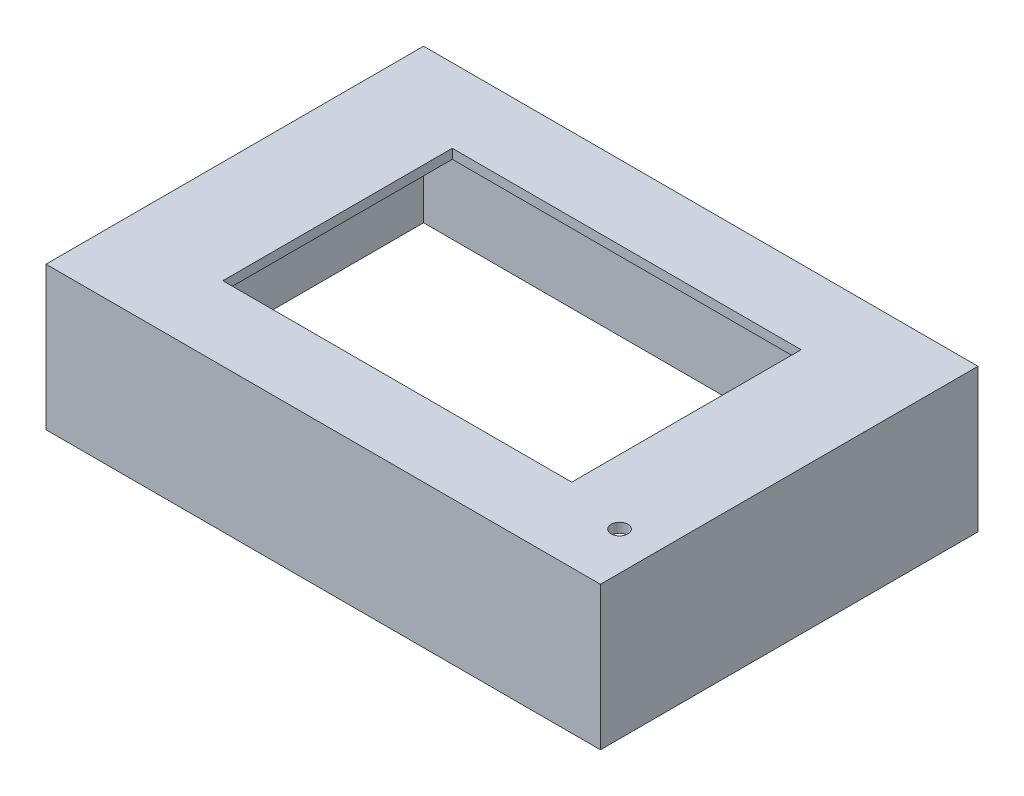
SolidWorks part; units mm, degrees
ref_plane "Front Plane" through (0, 0, 0) normal (0, 0, 1) x (1, 0, 0)
ref_plane "Top Plane" through (0, 0, 0) normal (0, 1, 0) x (1, 0, 0)
ref_plane "Right Plane" through (0, 0, 0) normal (1, 0, 0) x (0, 0, -1)
sketch "Sketch1" plane through (0, 0, 0) normal (0, 1, 0) x (1, 0, 0)
  line L0 (58, 39.5) -> (-58, 39.5)
  line L1 (56, -37.5) -> (-56, -37.5)
  line L2 (56, -37.5) -> (56, 37.5)
  line L3 (56, 37.5) -> (-56, 37.5)
  line L4 (-56, -37.5) -> (-56, 37.5)
  line L5 (56, -37.5) -> (-56, 37.5) construction
  line L6 (56, 37.5) -> (-56, -37.5) construction
  line L7 (-58, -39.5) -> (-58, 39.5)
  line L8 (58, -39.5) -> (-58, -39.5)
  line L9 (58, -39.5) -> (58, 39.5)
  point P0 (0, 0)
  dimension "D1" = 112
  dimension "D2" = 75
  dimension "D3" = 2
extrude "Boss-Extrude1" add sketch "Sketch1" along normal blind 28
sketch "Sketch2" plane through (0, 28, 0) normal (0, 1, 0) x (1, 0, 0)
  line L1 (58, -39.5) -> (-58, -39.5)
  line L2 (58, -39.5) -> (58, 39.5)
  line L3 (58, 39.5) -> (-58, 39.5)
  line L4 (-58, -39.5) -> (-58, 39.5)
  line L5 (58, -39.5) -> (-58, 39.5) construction
  line L6 (58, 39.5) -> (-58, -39.5) construction
  point P0 (0, 0)
extrude "Boss-Extrude2" add sketch "Sketch2" along normal blind 2
sketch "Sketch3" plane through (0, 30, 0) normal (0, 1, 0) x (1, 0, 0)
  line L1 (-36.5, 24) -> (36.5, 24)
  line L2 (-36.5, 24) -> (-36.5, -24)
  line L3 (-36.5, -24) -> (36.5, -24)
  line L4 (36.5, 24) -> (36.5, -24)
  line L5 (-36.5, 24) -> (36.5, -24) construction
  line L6 (-36.5, -24) -> (36.5, 24) construction
  point P0 (0, 0)
  dimension "D1" = 48
  dimension "D2" = 73
extrude "Cut-Extrude1" cut sketch "Sketch3" against normal up to surface (2 mm away) up to face at (0, 28, 0)
sketch "Sketch4" plane through (0, 30, 0) normal (0, 1, 0) x (1, 0, 0)
  line L0 (-58, -39.5) -> (58, -39.5) construction
  line L1 (58, -39.5) -> (58, 39.5) construction
  circle A0 centre (50, -27.5) radius 1.75
  dimension "D1" = 3.5
  dimension "D2" = 12
  dimension "D3" = 8
extrude "Cut-Extrude2" cut sketch "Sketch4" against normal up to surface (2 mm away) up to face at (0, 28, 0)
